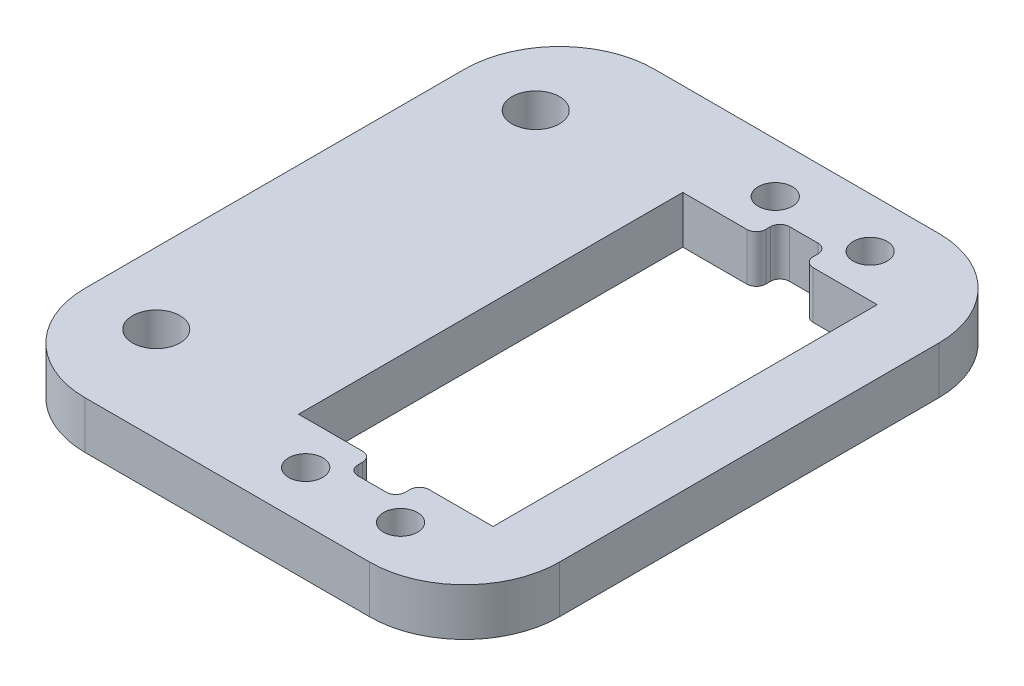
SolidWorks part; units mm, degrees
ref_plane "Front Plane" through (0, 0, 0) normal (0, 0, 1) x (1, 0, 0)
ref_plane "Top Plane" through (0, 0, 0) normal (0, 1, 0) x (1, 0, 0)
ref_plane "Right Plane" through (0, 0, 0) normal (1, 0, 0) x (0, 0, -1)
sketch "Sketch1" plane through (0, 0, 0) normal (0, 1, 0) x (1, 0, 0)
  line L1 (25, -30) -> (-25, -30)
  line L2 (25, -30) -> (25, 30)
  line L3 (25, 30) -> (-25, 30)
  line L4 (-25, -30) -> (-25, 30)
  line L5 (25, -30) -> (-25, 30) construction
  line L6 (25, 30) -> (-25, -30) construction
  point P0 (0, 0)
  dimension "D1" = 50
  dimension "D2" = 60
extrude "Boss-Extrude1" add sketch "Sketch1" along normal blind 5
sketch "Sketch2" plane through (0, 5, 0) normal (0, 1, 0) x (1, 0, 0)
  line L1 (18.25, -20.25) -> (-2.25, -20.25)
  line L2 (18.25, -20.25) -> (18.25, 20.25)
  line L3 (18.25, 20.25) -> (-2.25, 20.25)
  line L4 (-2.25, -20.25) -> (-2.25, 20.25)
  line L5 (18.25, -20.25) -> (-2.25, 20.25) construction
  line L6 (18.25, 20.25) -> (-2.25, -20.25) construction
  point P0 (8, 0)
  dimension "D1" = 20.5
  dimension "D2" = 40.5
  dimension "D3" = 0
  dimension "D4" = 8
extrude "Cut-Extrude1" cut sketch "Sketch2" against normal blind 5
sketch "Sketch3" plane through (0, 5, 0) normal (0, 1, 0) x (1, 0, 0)
  line L0 (8, 20.25) -> (8, -20.25) construction
  line L1 (18.25, 20.25) -> (-2.25, 20.25) construction
  line L2 (-2.25, -20.25) -> (18.25, -20.25) construction
  line L3 (-55, 0) -> (55, 0) construction
  circle A0 centre (3, 24.75) radius 1.8
  circle A1 centre (13, 24.75) radius 1.8
  circle A2 centre (13, -24.75) radius 1.8
  circle A3 centre (3, -24.75) radius 1.8
  dimension "D1" = 5
  dimension "D2" = 10
  dimension "D3" = 24.75
extrude "Cut-Extrude2" cut sketch "Sketch3" against normal blind 5
sketch "Sketch4" plane through (0, 5, 0) normal (0, 1, 0) x (1, 0, 0)
  line L0 (25, 30) -> (-25, 30) construction
  line L1 (-25, 30) -> (-25, -30) construction
  line L2 (-25, -30) -> (25, -30) construction
  circle A0 centre (-17.5, 20) radius 2.5
  circle A1 centre (-17.5, -20) radius 2.5
  dimension "D1" = 10
  dimension "D2" = 7.5
  dimension "D3" = 10
  dimension "D4" = 7.5
extrude "Cut-Extrude3" cut sketch "Sketch4" against normal blind 5
fillet "Fillet1" radius 10 4 edges at (25, 2.5, 30) (-25, 2.5, 30) (-25, 2.5, -30) (25, 2.5, -30)
sketch "Sketch5" plane through (0, 5, 0) normal (0, 1, 0) x (1, 0, 0)
  line L0 (18.25, 20.25) -> (-2.25, 20.25) construction
  line L1 (10.5, 17.75) -> (5.5, 17.75)
  line L2 (10.5, 17.75) -> (10.5, 22.75)
  line L3 (10.5, 22.75) -> (5.5, 22.75)
  line L4 (5.5, 17.75) -> (5.5, 22.75)
  line L5 (10.5, 17.75) -> (5.5, 22.75) construction
  line L6 (10.5, 22.75) -> (5.5, 17.75) construction
  point P0 (8, 20.25)
  dimension "D1" = 5
  dimension "D2" = 5
extrude "Cut-Extrude4" cut sketch "Sketch5" against normal blind 10
mirror "Mirror1" about plane through (0, 0, 0) normal (0, 0, 1) of "Cut-Extrude4"
fillet "Fillet2" radius 1 8 edges at (5.5, 2.5, 20.25) (10.5, 2.5, 20.25) (10.5, 2.5, 22.75) (5.5, 2.5, 22.75) (10.5, 2.5, -20.25) (10.5, 2.5, -22.75) (5.5, 2.5, -22.75) (5.5, 2.5, -20.25)
